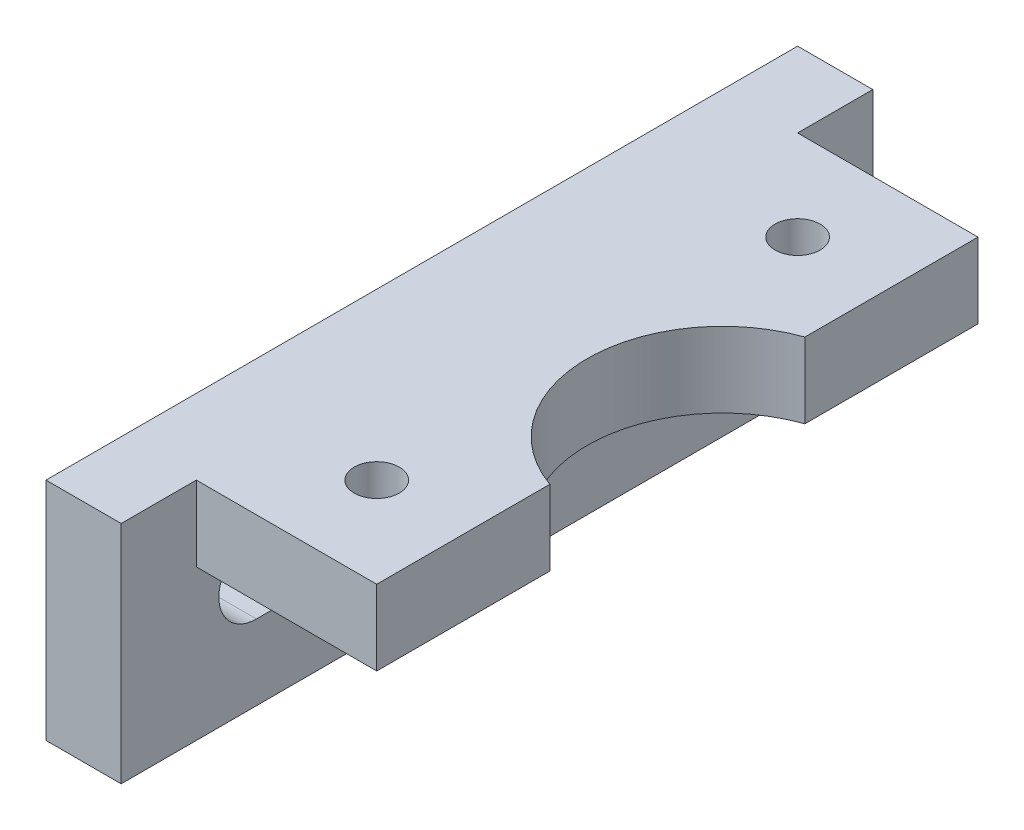
SolidWorks part; units mm, degrees
ref_plane "前视基准面" through (0, 0, 0) normal (0, 0, 1) x (1, 0, 0)
ref_plane "上视基准面" through (0, 0, 0) normal (0, 1, 0) x (1, 0, 0)
ref_plane "右视基准面" through (0, 0, 0) normal (1, 0, 0) x (0, 0, -1)
sketch "草图1" plane through (0, 0, 0) normal (-1, 0, 0) x (0, 0, 1)
  line L0 (-16, 0) -> (16, 0) construction
  line L1 (-25, 7.5) -> (25, 7.5)
  line L2 (-25, 7.5) -> (-25, -7.5)
  line L3 (-25, -7.5) -> (25, -7.5)
  line L4 (25, 7.5) -> (25, -7.5)
  line L5 (0, -7.5) -> (0, 7.5) construction
  line L6 (-25, 0) -> (25, 0) construction
  line L7 (-16, 2.5) -> (16, 2.5)
  line L8 (-16, -2.5) -> (16, -2.5)
  arc A0 (-16, 2.5) -> (-16, -2.5) centre (-16, 0) ccw
  arc A1 (16, -2.5) -> (16, 2.5) centre (16, 0) ccw
  point P0 (0, 0)
  point P6 (0, 0)
  point P14 (0, 0)
  point P15 (0, 0)
  point P16 (0, 0)
  dimension "D2" = 2.5
  dimension "D1" = 32
  dimension "D3" = 15
  dimension "D4" = 50
  dimension "D5" = 7.5
extrude "凸台-拉伸1" add sketch "草图1" along normal blind 5
sketch "草图2" plane through (0, 0, 0) normal (1, 0, 0) x (0, 0, -1)
  line L0 (44.9748, 0) -> (-44.7797, 0) construction
  line L1 (-25, 7.5) -> (25, 7.5) construction
  line L3 (-20, 7.5) -> (20, 7.5)
  line L4 (-20, 7.5) -> (-20, 2.5)
  line L5 (-20, 2.5) -> (20, 2.5)
  line L6 (20, 7.5) -> (20, 2.5)
  line L7 (0, 0) -> (0, 16.4675) construction
  point P9 (0, 0)
  dimension "D1" = 40
  dimension "D2" = 5
extrude "凸台-拉伸3" add sketch "草图2" along normal blind 12
sketch "草图3" plane through (0, 7.5, 0) normal (0, 1, 0) x (1, 0, 0)
  line L0 (-5, -25) -> (-5, 25) construction
  line L1 (12, 20) -> (0, 20) construction
  line L2 (12, -20) -> (0, -20) construction
  line L3 (12, 20) -> (12, -20) construction
  circle A1 centre (15, 0) radius 9
  circle A2 centre (6, 14) radius 1.5
  circle A3 centre (6, -14) radius 1.5
  dimension "D1" = 6
  dimension "D3" = 3
  dimension "D6" = 18
  dimension "D2" = 6
  dimension "D4" = 6
  dimension "D5" = 20
extrude "切除-拉伸1" cut sketch "草图3" against normal through all
